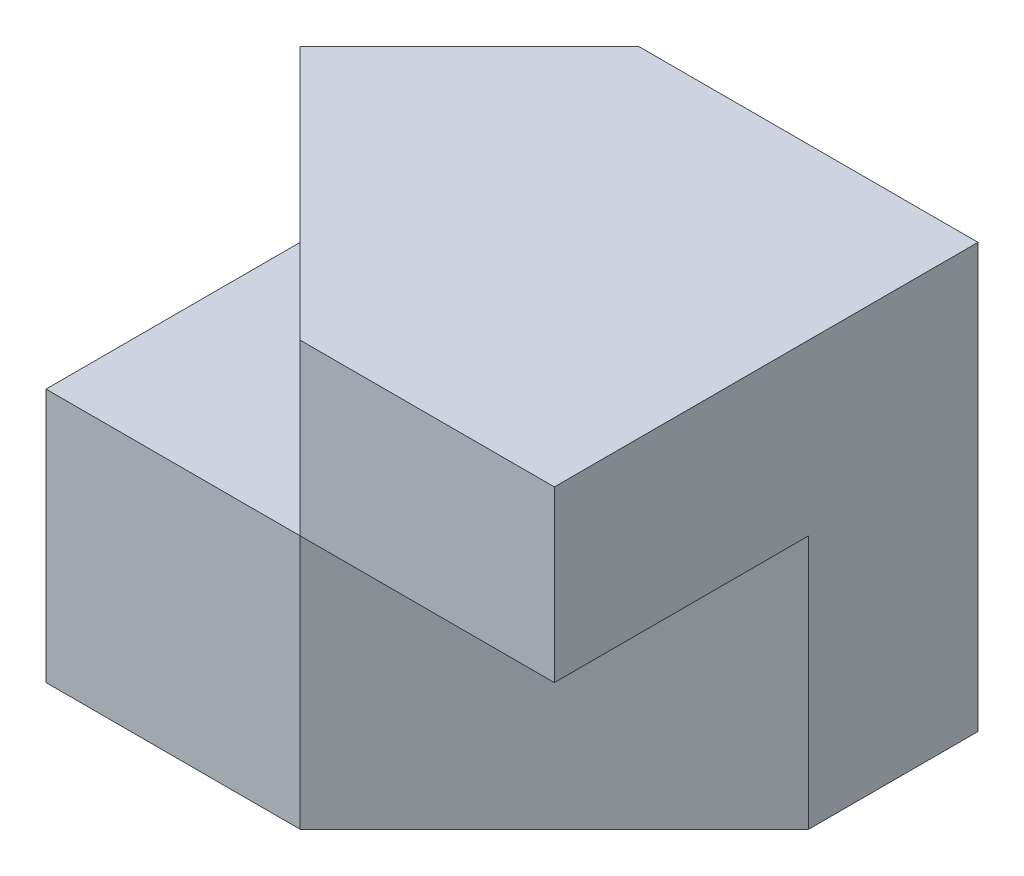
SolidWorks part; units mm, degrees
ref_plane "Front Plane" through (0, 0, 0) normal (0, 0, 1) x (1, 0, 0)
ref_plane "Top Plane" through (0, 0, 0) normal (0, 1, 0) x (1, 0, 0)
ref_plane "Right Plane" through (0, 0, 0) normal (1, 0, 0) x (0, 0, -1)
sketch "Sketch1" plane through (0, 0, 0) normal (0, 0, 1) x (1, 0, 0)
  line L1 (0, 0) -> (6, 0)
  line L2 (0, 0) -> (0, 5)
  line L3 (0, 5) -> (6, 5)
  line L4 (6, 0) -> (6, 5)
  dimension "D1" = 6
  dimension "D2" = 5
extrude "Boss-Extrude1" add sketch "Sketch1" along normal blind 5
sketch "Sketch4" plane through (0, 5, 0) normal (0, 1, 0) x (1, 0, 0)
  line L0 (0, -2) -> (2, 0)
  line L1 (0, -5) -> (0, 0) construction
  line L2 (6, 0) -> (0, 0) construction
  line L3 (2, 0) -> (0, 0)
  line L4 (0, 0) -> (0, -2)
  dimension "D1" = 2
  dimension "D2" = 2
extrude "Cut-Extrude1" cut sketch "Sketch4" against normal blind 5
sketch "Sketch5" plane through (0, 5, 0) normal (0, 1, 0) x (1, 0, 0)
  line L0 (0, -2) -> (3, -5)
  line L1 (6, -5) -> (0, -5) construction
  line L2 (3, -5) -> (0, -5)
  line L3 (0, -5) -> (0, -2)
extrude "Cut-Extrude2" cut sketch "Sketch5" against normal blind 2
sketch "Sketch6" plane through (0, 0, 0) normal (0, -1, 0) x (1, 0, 0)
  line L0 (6, 5) -> (3, 5)
  line L1 (0, 5) -> (6, 5) construction
  line L2 (3, 5) -> (6, 2)
  line L3 (6, 5) -> (6, 0) construction
  line L4 (6, 2) -> (6, 5)
  dimension "D1" = 3
extrude "Cut-Extrude3" cut sketch "Sketch6" against normal blind 3
